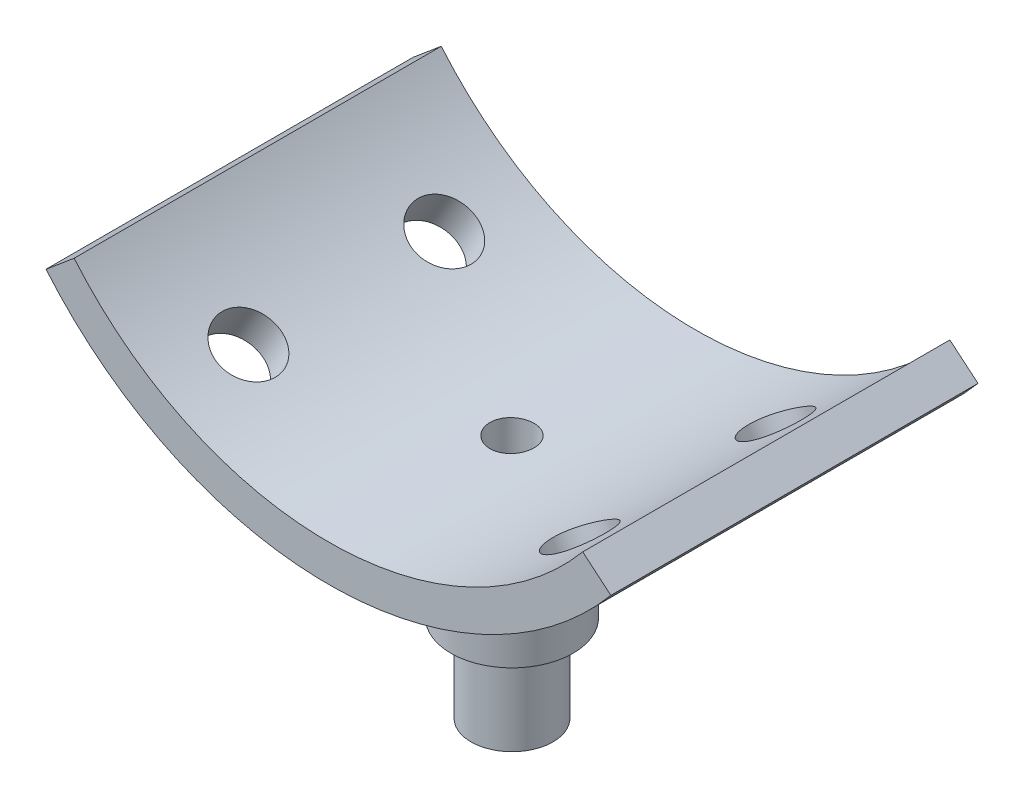
SolidWorks part; units mm, degrees
ref_plane "Front Plane" through (0, 0, 0) normal (0, 0, 1) x (1, 0, 0)
ref_plane "Top Plane" through (0, 0, 0) normal (0, 1, 0) x (1, 0, 0)
ref_plane "Right Plane" through (0, 0, 0) normal (1, 0, 0) x (0, 0, -1)
sketch "Sketch1" plane through (0, 0, 0) normal (0, 0, 1) x (1, 0, 0)
  line L0 (0, 31.2519) -> (0, -31.2519) construction
  line L1 (0, 0) -> (-23.0771, -19.364) construction
  line L2 (0, 0) -> (23.0771, -19.364) construction
  line L3 (23.0771, -19.364) -> (20.779, -17.4356)
  line L4 (-23.0771, -19.364) -> (-20.779, -17.4356)
  arc A0 (-20.779, -17.4356) -> (20.779, -17.4356) centre (0, 0) ccw
  arc A1 (-23.0771, -19.364) -> (23.0771, -19.364) centre (0, 0) ccw
  circle A2 centre (0, 0) radius 30.125 construction
  circle A3 centre (0, 0) radius 27.125 construction
  point P8 (0, 0)
  dimension "D1" = 54.25
  dimension "D3" = 50
  dimension "D2" = 3
extrude "Boss-Extrude1" add sketch "Sketch1" along normal mid plane 30
ref_plane "Plane1" through (0, -40, 0) normal (0, 1, 0) x (1, 0, 0)
sketch "Sketch2" plane through (0, -40, 0) normal (0, 1, 0) x (1, 0, 0)
  circle A0 centre (0, 0) radius 5
  dimension "D1" = 10
extrude "Boss-Extrude2" add sketch "Sketch2" along normal up to surface (9.875 mm away)
sketch "Sketch5" plane through (0, 0, 0) normal (0, 0, 1) x (1, 0, 0)
  line L0 (0, 0) -> (15.0625, -26.089) construction
  line L1 (0, 14.0723) -> (0, -38.9472) construction
  line L2 (0, 0) -> (-15.0625, -26.089) construction
  arc A0 (-23.0771, -19.364) -> (23.0771, -19.364) centre (0, 0) ccw construction
  dimension "D1" = 30
ref_plane "Plane3" through (15.0625, -26.089, 0) normal (0.5, -0.866, 0) x (-0.866, -0.5, 0)
sketch "Sketch13" plane through (15.0625, -26.089, 0) normal (0.5, -0.866, 0) x (-0.866, -0.5, 0)
  line L0 (-17.4465, 0) -> (25.4678, 0) construction
  circle A1 centre (0, 8) radius 2.5
  circle A2 centre (0, -8) radius 2.5
  dimension "D1" = 5
  dimension "D2" = 8
extrude "Cut-Extrude2" cut sketch "Sketch13" against normal through all
mirror "Mirror1" about plane through (0, 0, 0) normal (1, 0, 0) of "Cut-Extrude2"
sketch "Sketch14" plane through (0, -40, 0) normal (0, -1, 0) x (1, 0, 0)
  circle A0 centre (0, 0) radius 3.35
  dimension "D1" = 6.7
extrude "Boss-Extrude4" add sketch "Sketch14" along normal blind 7.1
sketch "Sketch4" plane through (0, -40, 0) normal (0, -1, 0) x (1, 0, 0)
  line L0 (-6.6, 0) -> (6.6, 0) construction
  line L5 (-6.6, 0.8) -> (-4.9356, 0.8)
  line L6 (-6.6, 0.8) -> (-6.6, -0.8)
  line L7 (-6.6, -0.8) -> (-4.9356, -0.8)
  line L8 (6.6, 0.8) -> (6.6, -0.8)
  line L9 (0, 12.2903) -> (0, -12.2903) construction
  line L10 (4.9356, 0.8) -> (6.6, 0.8)
  line L11 (4.9356, -0.8) -> (6.6, -0.8)
  circle A0 centre (0, 0) radius 5 construction
  arc A1 (-4.9356, 0.8) -> (-4.9356, -0.8) centre (0, 0) ccw
  arc A2 (4.9356, -0.8) -> (4.9356, 0.8) centre (0, 0) ccw
  point P10 (0, 0)
  point P11 (0, 0)
  point P12 (6.6, 0)
  point P20 (5, 0)
  dimension "D1" = 1.6
  dimension "D2" = 1.6
sketch "Sketch15" plane through (0, -47.1, 0) normal (0, -1, 0) x (1, 0, 0)
  circle A0 centre (0, 0) radius 1.8
  dimension "D1" = 3.6
extrude "Cut-Extrude3" cut sketch "Sketch15" against normal through all
